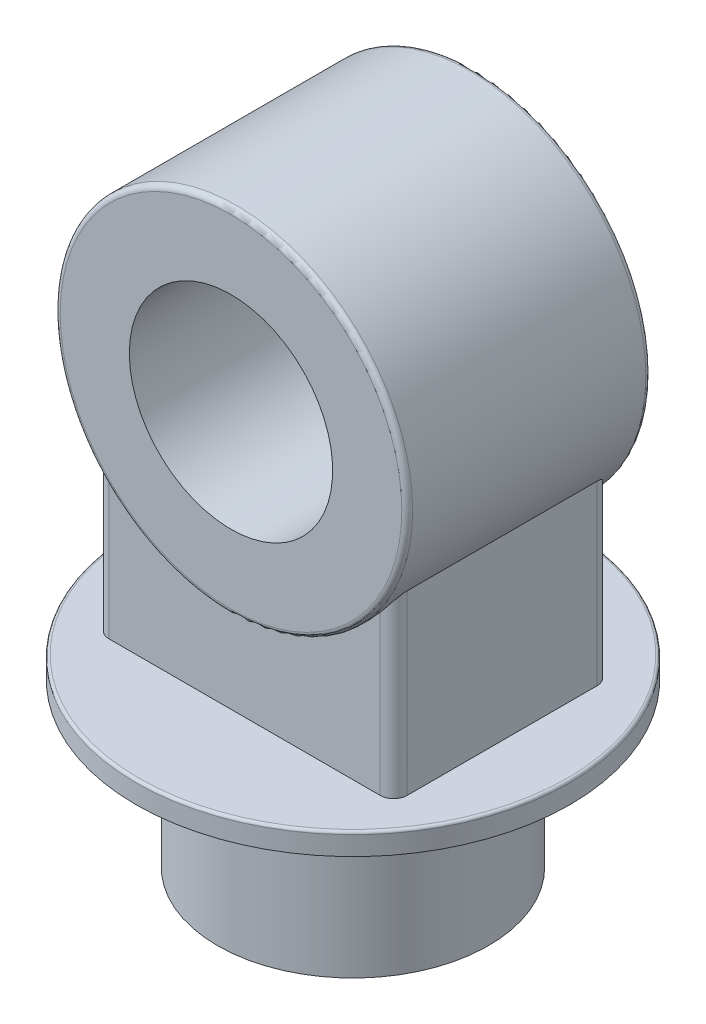
SolidWorks part; units mm, degrees
ref_plane "Front Plane" through (0, 0, 0) normal (0, 0, 1) x (1, 0, 0)
ref_plane "Top Plane" through (0, 0, 0) normal (0, 1, 0) x (1, 0, 0)
ref_plane "Right Plane" through (0, 0, 0) normal (1, 0, 0) x (0, 0, -1)
sketch "Sketch1" plane through (0, 0, 0) normal (0, 1, 0) x (1, 0, 0)
  circle A0 centre (0, 0) radius 100
  dimension "D1" = 200
extrude "Boss-Extrude1" add sketch "Sketch1" along normal blind 120
sketch "Sketch2" plane through (0, 120, 0) normal (0, 1, 0) x (1, 0, 0)
  circle A0 centre (0, 0) radius 160
  dimension "D1" = 320
extrude "Boss-Extrude2" add sketch "Sketch2" along normal blind 16
sketch "Sketch3" plane through (0, 0, 0) normal (0, 0, 1) x (1, 0, 0)
  line L0 (160, 136) -> (-160, 136) construction
  circle A0 centre (0, 336) radius 75
  circle A1 centre (0, 336) radius 130
  dimension "D1" = 150
  dimension "D2" = 260
  dimension "D3" = 200
extrude "Boss-Extrude3" add sketch "Sketch3" along normal mid plane 180 separate body
sketch "Sketch4" plane through (0, 136, 0) normal (0, 1, 0) x (1, 0, 0)
  line L1 (110, -80) -> (-110, -80)
  line L2 (110, -80) -> (110, 80)
  line L3 (110, 80) -> (-110, 80)
  line L4 (-110, -80) -> (-110, 80)
  line L5 (110, -80) -> (-110, 80) construction
  line L6 (110, 80) -> (-110, -80) construction
  point P0 (0, 0)
  dimension "D1" = 220
  dimension "D2" = 160
extrude "Boss-Extrude4" add sketch "Sketch4" along normal up to next
fillet "Fillet1" radius 2 1 edges at (0, 136, 160)
fillet "Fillet2" radius 4 2 edges at (130, 336, -90) (130, 336, 90)
fillet "Fillet3" radius 10 4 edges at (-110, 201.359, -80) (-110, 201.359, 80) (110, 201.359, -80) (110, 201.359, 80)
